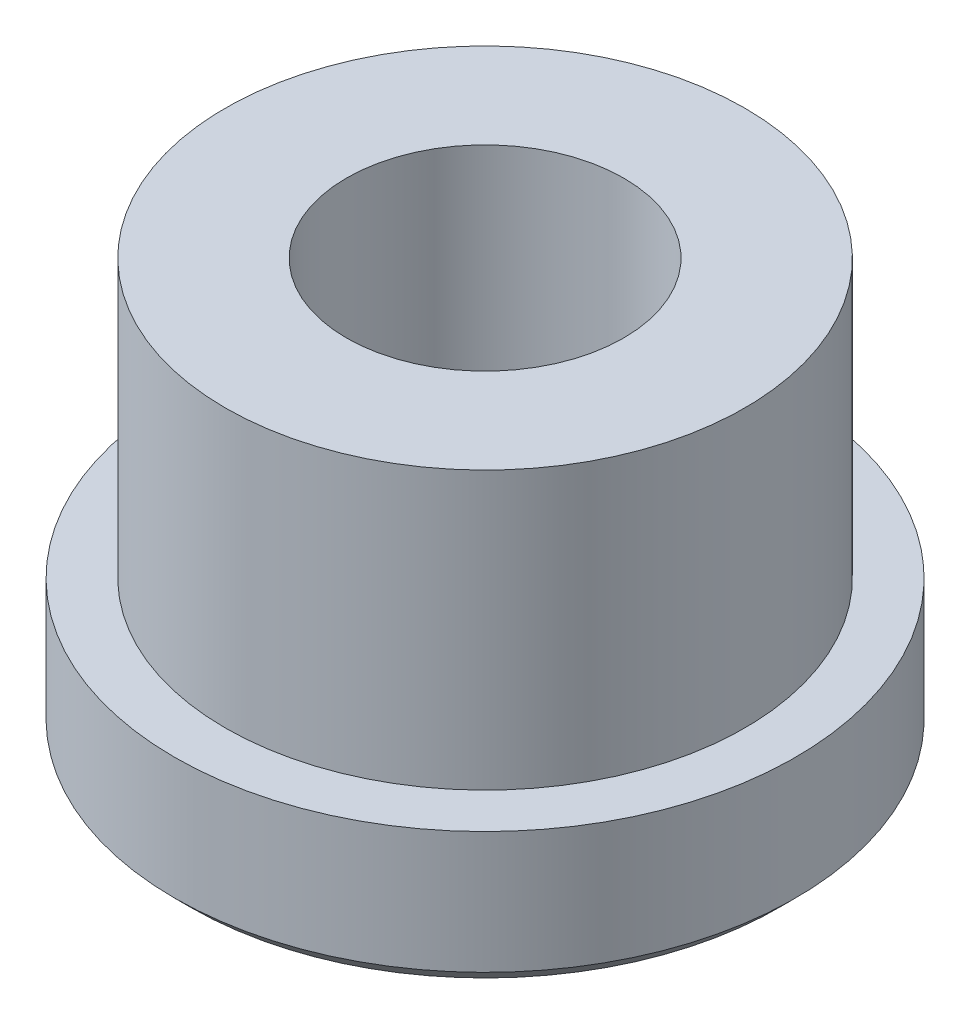
SolidWorks part; units mm, degrees
material "Brass"
ref_plane "Front Plane" through (0, 0, 0) normal (0, 0, 1) x (1, 0, 0)
ref_plane "Top Plane" through (0, 0, 0) normal (0, 1, 0) x (1, 0, 0)
ref_plane "Right Plane" through (0, 0, 0) normal (1, 0, 0) x (0, 0, -1)
sketch "Sketch2" plane through (0, 0, 0) normal (0, 0, 1) x (1, 0, 0)
  line L0 (0, 0) -> (0, -50000) construction
  line L1 (0, 0) -> (14.224, 0) construction
  line L2 (14.224, 0) -> (14.224, 6.35)
  line L3 (14.224, 6.35) -> (11.8999, 6.35)
  line L4 (11.8999, 6.35) -> (11.8999, 19.05)
  line L5 (11.8999, 19.05) -> (0, 19.05) construction
  line L6 (11.8999, 19.05) -> (6.35, 19.05)
  line L7 (6.35, 19.05) -> (6.35, 0)
  line L8 (6.35, 0) -> (14.224, 0)
  dimension "D1" = 19.05
  dimension "D2" = 12.7
  dimension "D3" = 14.224
  dimension "D4" = 11.8999
  dimension "D5" = 12.7
revolve "Revolve1" add sketch "Sketch2" angle 360 about L0
cosmetic thread "Cosmetic Thread1" parameters "D2"=38.1
cosmetic thread "Cosmetic Thread2" parameters "D2"=22.7998
chamfer "Chamfer1" distance 0.762 angle 45 1 edges at (0, 0, 14.224)
